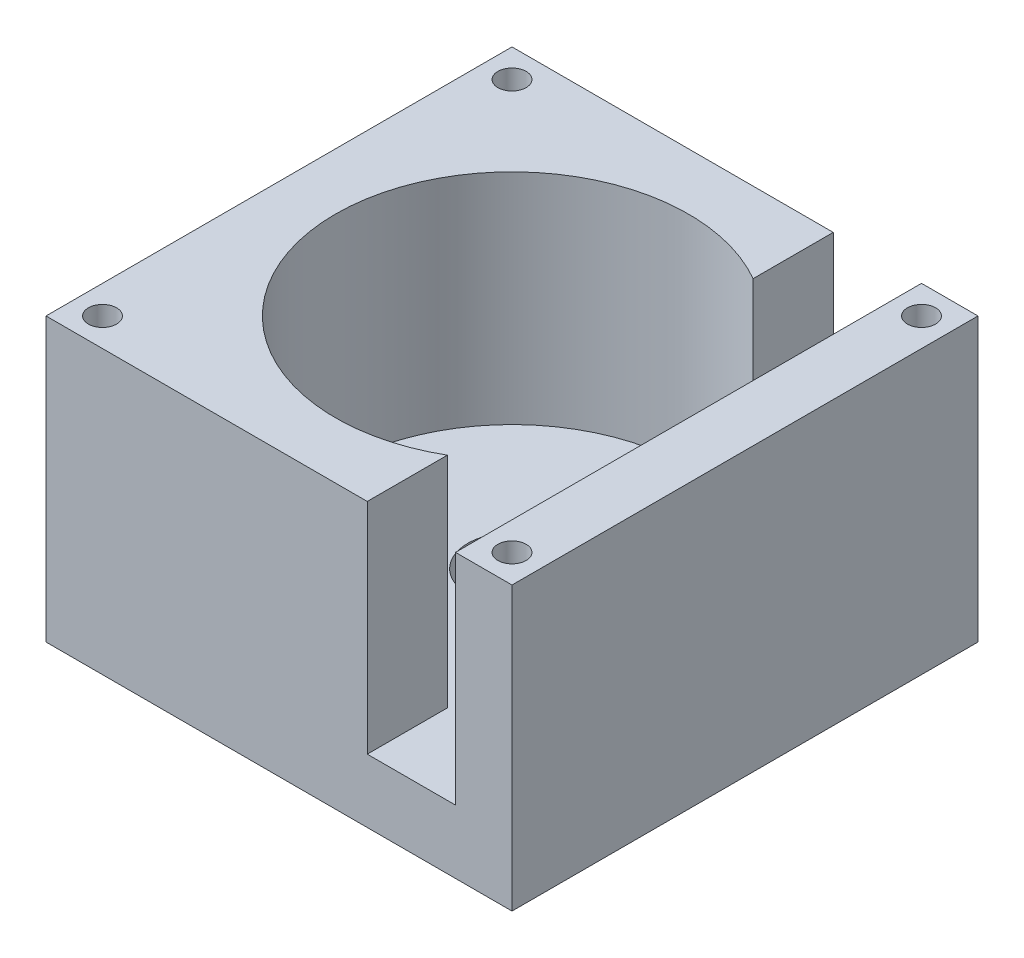
SolidWorks part; units mm, degrees
ref_plane "Front Plane" through (0, 0, 0) normal (0, 0, 1) x (1, 0, 0)
ref_plane "Top Plane" through (0, 0, 0) normal (0, 1, 0) x (1, 0, 0)
ref_plane "Right Plane" through (0, 0, 0) normal (1, 0, 0) x (0, 0, -1)
sketch "Sketch1" plane through (0, 0, 0) normal (0, 1, 0) x (1, 0, 0)
  line L1 (-33, -33) -> (33, -33)
  line L2 (-33, -33) -> (-33, 33)
  line L3 (-33, 33) -> (33, 33)
  line L4 (33, -33) -> (33, 33)
  line L5 (-33, -33) -> (33, 33) construction
  line L6 (-33, 33) -> (33, -33) construction
  point P0 (0, 0)
  dimension "D1" = 66
  dimension "D2" = 66
extrude "Boss-Extrude1" add sketch "Sketch1" along normal blind 40
sketch "Sketch2" plane through (0, 40, 0) normal (0, 1, 0) x (1, 0, 0)
  circle A0 centre (0, 0) radius 25
  dimension "D1" = 50
extrude "Cut-Extrude1" cut sketch "Sketch2" against normal blind 31
sketch "Sketch3" plane through (0, 9, 0) normal (0, 1, 0) x (1, 0, 0)
  circle A0 centre (0, 0) radius 6.25
  dimension "D1" = 12.5
extrude "Cut-Extrude2" cut sketch "Sketch3" against normal blind 7
sketch "Sketch4" plane through (0, 0, 33) normal (0, 0, 1) x (1, 0, 0)
  line L0 (25, 40) -> (25, 9)
  line L1 (25, 9) -> (12.5, 9)
  line L2 (25, 9) -> (-25, 9) construction
  line L3 (12.5, 9) -> (12.5, 40)
  line L4 (-33, 40) -> (33, 40) construction
  line L5 (12.5, 40) -> (25, 40)
  dimension "D1" = 12.5
extrude "Cut-Extrude3" cut sketch "Sketch4" against normal through all both and the other way through all
sketch "Sketch5" plane through (0, 40, 0) normal (0, 1, 0) x (1, 0, 0)
  line L0 (-33, 33) -> (-33, -33) construction
  line L1 (29, -29) -> (-29, -29) construction
  line L2 (29, -29) -> (29, 29) construction
  line L3 (29, 29) -> (-29, 29) construction
  line L4 (-29, -29) -> (-29, 29) construction
  line L5 (29, -29) -> (-29, 29) construction
  line L6 (29, 29) -> (-29, -29) construction
  line L7 (-33, -33) -> (12.5, -33) construction
  circle A0 centre (-29, -29) radius 2
  circle A1 centre (-29, 29) radius 2
  circle A2 centre (29, 29) radius 2
  circle A3 centre (29, -29) radius 2
  point P0 (0, 0)
  dimension "D3" = 4
  dimension "D4" = 4
  dimension "D5" = 4
  dimension "D6" = 4
  dimension "D1" = 4
  dimension "D2" = 4
extrude "Cut-Extrude4" cut sketch "Sketch5" against normal blind 10
